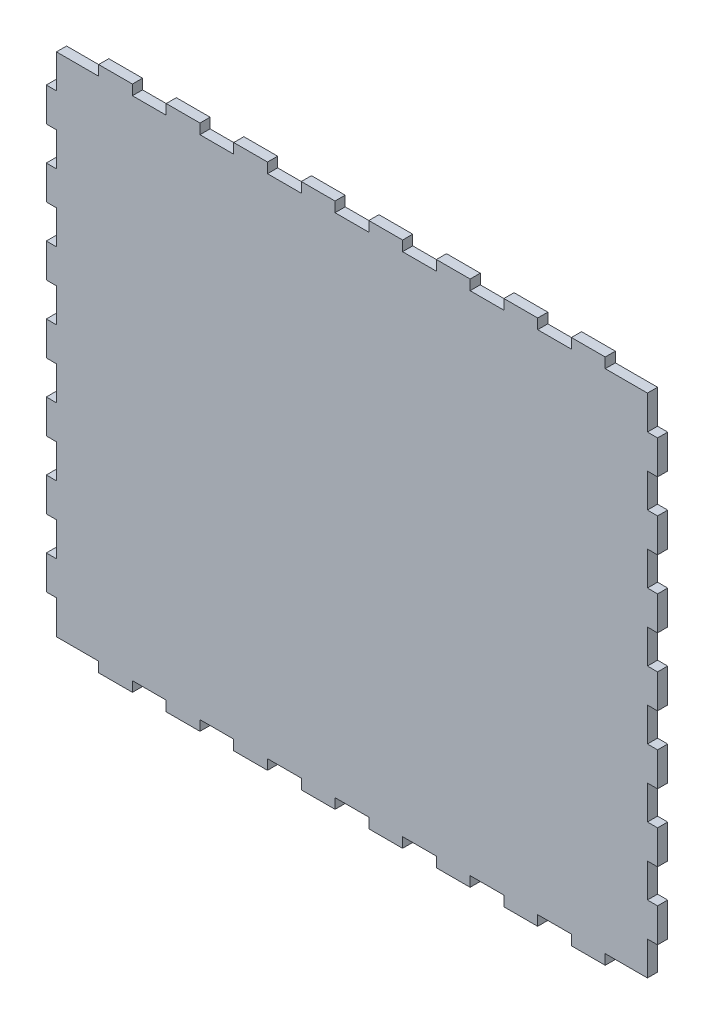
SolidWorks part; units mm, degrees
ref_plane "Front Plane" through (0, 0, 0) normal (0, 0, 1) x (1, 0, 0)
ref_plane "Top Plane" through (0, 0, 0) normal (0, 1, 0) x (1, 0, 0)
ref_plane "Right Plane" through (0, 0, 0) normal (1, 0, 0) x (0, 0, -1)
sketch "Sketch1" plane through (0, 0, 10) normal (0, 0, 1) x (1, 0, 0)
  line L0 (12.5, -13) -> (12.5, -10)
  line L3 (-10, -10) -> (2.5, -10)
  line L4 (-10, 140) -> (-10, -10)
  line L5 (-10, -10) -> (165, -10)
  line L6 (165, -10) -> (165, 140)
  line L7 (165, 140) -> (-10, 140)
  line L8 (-10, 140) -> (-10, -10) construction
  line L9 (-10, -10) -> (165, -10) construction
  line L10 (165, -10) -> (165, 140) construction
  line L11 (165, 140) -> (-10, 140) construction
  line L12 (2.5, -13) -> (2.5, -10)
  line L13 (12.5, -10) -> (22.5, -10)
  line L14 (22.5, -10) -> (22.5, -13)
  line L15 (32.5, -13) -> (32.5, -10)
  line L16 (-13, 143) -> (-13, -13)
  line L17 (-13, -13) -> (168, -13)
  line L18 (168, -13) -> (168, 143)
  line L19 (168, 143) -> (-13, 143)
  line L20 (-13, 130) -> (-13, 120)
  line L21 (2.5, -13) -> (12.5, -13)
  line L22 (168, 0) -> (168, 10)
  line L24 (32.5, -10) -> (42.5, -10)
  line L25 (42.5, -10) -> (42.5, -13)
  line L26 (52.5, -13) -> (52.5, -10)
  line L27 (52.5, -10) -> (62.5, -10)
  line L28 (62.5, -10) -> (62.5, -13)
  line L29 (72.5, -13) -> (72.5, -10)
  line L30 (72.5, -10) -> (82.5, -10)
  line L31 (82.5, -10) -> (82.5, -13)
  line L32 (92.5, -13) -> (92.5, -10)
  line L33 (92.5, -10) -> (102.5, -10)
  line L34 (102.5, -10) -> (102.5, -13)
  line L35 (112.5, -13) -> (112.5, -10)
  line L36 (112.5, -10) -> (122.5, -10)
  line L37 (122.5, -10) -> (122.5, -13)
  line L38 (132.5, -13) -> (132.5, -10)
  line L39 (132.5, -10) -> (142.5, -10)
  line L40 (142.5, -10) -> (142.5, -13)
  line L41 (22.5, -13) -> (32.5, -13)
  line L42 (42.5, -13) -> (52.5, -13)
  line L43 (62.5, -13) -> (72.5, -13)
  line L44 (82.5, -13) -> (92.5, -13)
  line L45 (102.5, -13) -> (112.5, -13)
  line L46 (122.5, -13) -> (132.5, -13)
  line L47 (142.5, -13) -> (152.5, -13)
  line L48 (165, -10) -> (152.5, -10)
  line L49 (152.5, -10) -> (152.5, -13)
  line L50 (-13, 143) -> (-27.3181, 143) construction
  line L51 (-27.3181, 143) -> (-27.3181, -13) construction
  line L52 (-27.3181, -13) -> (2.5, -13) construction
  line L53 (-27.3181, 65) -> (168, 65) construction
  line L54 (-27.3181, 143) -> (2.5, 143) construction
  line L55 (152.5, 140) -> (152.5, 143)
  line L56 (165, 140) -> (152.5, 140)
  line L57 (142.5, 143) -> (152.5, 143)
  line L58 (122.5, 143) -> (132.5, 143)
  line L59 (102.5, 143) -> (112.5, 143)
  line L60 (82.5, 143) -> (92.5, 143)
  line L61 (62.5, 143) -> (72.5, 143)
  line L62 (42.5, 143) -> (52.5, 143)
  line L63 (22.5, 143) -> (32.5, 143)
  line L64 (142.5, 140) -> (142.5, 143)
  line L65 (132.5, 140) -> (142.5, 140)
  line L66 (132.5, 143) -> (132.5, 140)
  line L67 (122.5, 140) -> (122.5, 143)
  line L68 (112.5, 140) -> (122.5, 140)
  line L69 (112.5, 143) -> (112.5, 140)
  line L70 (102.5, 140) -> (102.5, 143)
  line L71 (92.5, 140) -> (102.5, 140)
  line L72 (92.5, 143) -> (92.5, 140)
  line L73 (82.5, 140) -> (82.5, 143)
  line L74 (72.5, 140) -> (82.5, 140)
  line L75 (72.5, 143) -> (72.5, 140)
  line L76 (62.5, 140) -> (62.5, 143)
  line L77 (52.5, 140) -> (62.5, 140)
  line L78 (52.5, 143) -> (52.5, 140)
  line L79 (42.5, 140) -> (42.5, 143)
  line L80 (32.5, 140) -> (42.5, 140)
  line L81 (2.5, 143) -> (12.5, 143)
  line L82 (32.5, 143) -> (32.5, 140)
  line L83 (22.5, 140) -> (22.5, 143)
  line L84 (12.5, 140) -> (22.5, 140)
  line L85 (2.5, 143) -> (2.5, 140)
  line L86 (-10, 140) -> (2.5, 140)
  line L87 (12.5, 143) -> (12.5, 140)
  line L88 (77.5, 140) -> (77.5, -10) construction
  line L89 (-13, 0) -> (-10, 0)
  line L90 (-10, 0) -> (-10, -10)
  line L91 (-13, 10) -> (-10, 10)
  line L92 (-10, 10) -> (-10, 20)
  line L93 (-10, 20) -> (-13, 20)
  line L94 (-13, 10) -> (-13, 0)
  line L95 (-10, 40) -> (-13, 40)
  line L96 (-10, 30) -> (-10, 40)
  line L97 (-13, 30) -> (-10, 30)
  line L98 (-10, 60) -> (-13, 60)
  line L99 (-10, 50) -> (-10, 60)
  line L100 (-13, 50) -> (-10, 50)
  line L101 (-10, 80) -> (-13, 80)
  line L102 (-10, 70) -> (-10, 80)
  line L103 (-13, 70) -> (-10, 70)
  line L104 (-10, 100) -> (-13, 100)
  line L105 (-10, 90) -> (-10, 100)
  line L106 (-13, 90) -> (-10, 90)
  line L107 (-10, 120) -> (-13, 120)
  line L108 (-10, 110) -> (-10, 120)
  line L109 (-13, 110) -> (-10, 110)
  line L110 (-13, 30) -> (-13, 20)
  line L111 (-13, 50) -> (-13, 40)
  line L112 (-13, 70) -> (-13, 60)
  line L113 (-13, 90) -> (-13, 80)
  line L114 (-13, 110) -> (-13, 100)
  line L115 (-10, 140) -> (-10, 130)
  line L116 (-10, 130) -> (-13, 130)
  line L117 (165, 140) -> (165, 130)
  line L118 (165, 130) -> (168, 130)
  line L119 (168, 120) -> (165, 120)
  line L120 (165, 120) -> (165, 110)
  line L121 (165, 110) -> (168, 110)
  line L122 (168, 120) -> (168, 130)
  line L123 (168, 100) -> (165, 100)
  line L124 (165, 100) -> (165, 90)
  line L125 (165, 90) -> (168, 90)
  line L126 (168, 80) -> (165, 80)
  line L127 (165, 80) -> (165, 70)
  line L128 (165, 70) -> (168, 70)
  line L129 (168, 60) -> (165, 60)
  line L130 (165, 60) -> (165, 50)
  line L131 (165, 50) -> (168, 50)
  line L132 (168, 40) -> (165, 40)
  line L133 (165, 40) -> (165, 30)
  line L134 (165, 30) -> (168, 30)
  line L135 (168, 20) -> (165, 20)
  line L136 (165, 20) -> (165, 10)
  line L137 (165, 10) -> (168, 10)
  line L138 (168, 100) -> (168, 110)
  line L139 (168, 80) -> (168, 90)
  line L140 (168, 60) -> (168, 70)
  line L141 (168, 40) -> (168, 50)
  line L142 (168, 20) -> (168, 30)
  line L143 (168, 0) -> (165, 0)
  line L144 (165, 0) -> (165, -10)
  dimension "D3" = 15.5
  dimension "D4" = 10
  dimension "D5" = 10
  dimension "D7" = 10
  dimension "D8" = 10
  dimension "D9" = 10
  dimension "D10" = 10
  dimension "D12" = 10
  dimension "D13" = 10
  dimension "D14" = 10
  dimension "D15" = 10
  dimension "D17" = 10
  dimension "D18" = 10
  dimension "D1" = 0
  dimension "D2" = 3
  dimension "D6" = 7
  dimension "D11" = 6
  dimension "D16" = 6
extrude "Boss-Extrude1" add sketch "Sketch1" along normal blind 3
